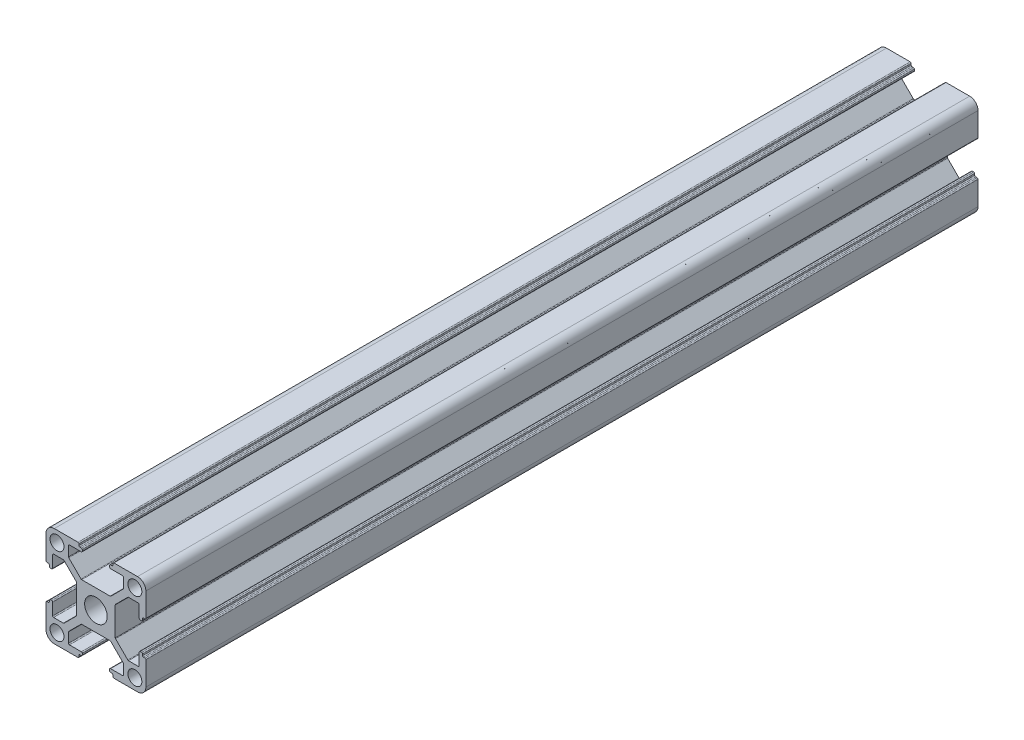
SolidWorks part; units mm, degrees
ref_plane "Alzado" through (0, 0, 0) normal (0, 0, 1) x (1, 0, 0)
ref_plane "Planta" through (0, 0, 0) normal (0, 1, 0) x (1, 0, 0)
ref_plane "Vista lateral" through (0, 0, 0) normal (1, 0, 0) x (0, 0, -1)
ref_plane "Plano1" through (0, 0, -50) normal (0, 0, -1) x (-1, 0, 0)
sketch "Croquis1" plane through (0, 0, -50) normal (0, 0, -1) x (-1, 0, 0)
  line L0 (14.7, -5.1) -> (14.3, -5.1)
  line L1 (14, -4.8) -> (14, -4.4)
  line L2 (13.7, -4.1) -> (13.3, -4.1)
  line L3 (13, -4.4) -> (13, -7.95)
  line L4 (12.7, -8.25) -> (9.7893, -8.25)
  line L5 (9.5772, -8.1622) -> (5.8879, -4.4739)
  line L6 (5.8, -4.2617) -> (5.8, 4.2607)
  line L7 (5.8879, 4.4729) -> (9.5771, 8.1621)
  line L8 (9.7893, 8.25) -> (12.7, 8.25)
  line L9 (13, 7.95) -> (13, 4.4)
  line L10 (13.3, 4.1) -> (13.7, 4.1)
  line L11 (14, 4.4) -> (14, 4.8)
  line L12 (14.3, 5.1) -> (14.7, 5.1)
  line L13 (15, 5.4) -> (15, 12.5)
  line L14 (12.5, 15) -> (5.4, 15)
  line L15 (5.1, 14.7) -> (5.1, 14.3)
  line L16 (4.8, 14) -> (4.4, 14)
  line L17 (4.1, 13.7) -> (4.1, 13.3)
  line L18 (4.4, 13) -> (7.95, 13)
  line L19 (8.25, 12.7) -> (8.25, 9.7883)
  line L20 (8.1621, 9.5761) -> (4.4739, 5.8879)
  line L21 (4.2617, 5.8) -> (-4.2607, 5.8)
  line L22 (-4.4728, 5.8878) -> (-8.1621, 9.5761)
  line L23 (-8.25, 9.7883) -> (-8.25, 12.7)
  line L24 (-7.95, 13) -> (-4.4, 13)
  line L25 (-4.1, 13.3) -> (-4.1, 13.7)
  line L26 (-4.4, 14) -> (-4.8, 14)
  line L27 (-5.1, 14.3) -> (-5.1, 14.7)
  line L28 (-5.4, 15) -> (-12.5, 15)
  line L29 (-15, 12.5) -> (-15, 5.4)
  line L30 (-14.7, 5.1) -> (-14.3, 5.1)
  line L31 (-14, 4.8) -> (-14, 4.4)
  line L32 (-13.7, 4.1) -> (-13.3, 4.1)
  line L33 (-13, 4.4) -> (-13, 7.95)
  line L34 (-12.7, 8.25) -> (-9.7883, 8.25)
  line L35 (-9.5761, 8.1621) -> (-5.8878, 4.4728)
  line L36 (-5.8, 4.2607) -> (-5.8, -4.2617)
  line L37 (-5.8879, -4.4739) -> (-9.5761, -8.1621)
  line L38 (-9.7883, -8.25) -> (-12.7, -8.25)
  line L39 (-13, -7.95) -> (-13, -4.4)
  line L40 (-13.3, -4.1) -> (-13.7, -4.1)
  line L41 (-14, -4.4) -> (-14, -4.8)
  line L42 (-14.3, -5.1) -> (-14.7, -5.1)
  line L43 (-15, -5.4) -> (-15, -12.5)
  line L44 (-12.5, -15) -> (-5.4, -15)
  line L45 (-5.1, -14.7) -> (-5.1, -14.3)
  line L46 (-4.8, -14) -> (-4.4, -14)
  line L47 (-4.1, -13.7) -> (-4.1, -13.3)
  line L48 (-4.4, -13) -> (-7.95, -13)
  line L49 (-8.25, -12.7) -> (-8.25, -9.7893)
  line L50 (-8.1621, -9.5771) -> (-4.4729, -5.8879)
  line L51 (-4.2607, -5.8) -> (4.2617, -5.8)
  line L52 (4.4739, -5.8879) -> (8.1622, -9.5772)
  line L53 (8.25, -9.7893) -> (8.25, -12.7)
  line L54 (7.95, -13) -> (4.4, -13)
  line L55 (4.1, -13.3) -> (4.1, -13.7)
  line L56 (4.4, -14) -> (4.8, -14)
  line L57 (5.1, -14.3) -> (5.1, -14.7)
  line L58 (5.4, -15) -> (12.5, -15)
  line L59 (15, -12.5) -> (15, -5.4)
  arc A0 (15, -5.4) -> (14.7, -5.1) centre (14.7, -5.4) ccw
  arc A1 (14.3, -5.1) -> (14, -4.8) centre (14.3, -4.8) cw
  arc A2 (14, -4.4) -> (13.7, -4.1) centre (13.7, -4.4) ccw
  arc A3 (13.3, -4.1) -> (13, -4.4) centre (13.3, -4.4) ccw
  arc A4 (13, -7.95) -> (12.7, -8.25) centre (12.7, -7.95) cw
  arc A5 (9.7893, -8.25) -> (9.5772, -8.1622) centre (9.7893, -7.95) cw
  arc A6 (5.8879, -4.4739) -> (5.8, -4.2617) centre (6.1, -4.2617) cw
  arc A7 (5.8, 4.2607) -> (5.8879, 4.4729) centre (6.1, 4.2607) cw
  arc A8 (9.5771, 8.1621) -> (9.7893, 8.25) centre (9.7893, 7.95) cw
  arc A9 (12.7, 8.25) -> (13, 7.95) centre (12.7, 7.95) cw
  arc A10 (13, 4.4) -> (13.3, 4.1) centre (13.3, 4.4) ccw
  arc A11 (13.7, 4.1) -> (14, 4.4) centre (13.7, 4.4) ccw
  arc A12 (14, 4.8) -> (14.3, 5.1) centre (14.3, 4.8) cw
  arc A13 (14.7, 5.1) -> (15, 5.4) centre (14.7, 5.4) ccw
  arc A14 (15, 12.5) -> (12.5, 15) centre (12.5, 12.5) ccw
  arc A15 (5.4, 15) -> (5.1, 14.7) centre (5.4, 14.7) ccw
  arc A16 (5.1, 14.3) -> (4.8, 14) centre (4.8, 14.3) cw
  arc A17 (4.4, 14) -> (4.1, 13.7) centre (4.4, 13.7) ccw
  arc A18 (4.1, 13.3) -> (4.4, 13) centre (4.4, 13.3) ccw
  arc A19 (7.95, 13) -> (8.25, 12.7) centre (7.95, 12.7) cw
  arc A20 (8.25, 9.7883) -> (8.1621, 9.5761) centre (7.95, 9.7883) cw
  arc A21 (4.4739, 5.8879) -> (4.2617, 5.8) centre (4.2617, 6.1) cw
  arc A22 (-4.2607, 5.8) -> (-4.4728, 5.8878) centre (-4.2607, 6.1) cw
  arc A23 (-8.1621, 9.5761) -> (-8.25, 9.7883) centre (-7.95, 9.7883) cw
  arc A24 (-8.25, 12.7) -> (-7.95, 13) centre (-7.95, 12.7) cw
  arc A25 (-4.4, 13) -> (-4.1, 13.3) centre (-4.4, 13.3) ccw
  arc A26 (-4.1, 13.7) -> (-4.4, 14) centre (-4.4, 13.7) ccw
  arc A27 (-4.8, 14) -> (-5.1, 14.3) centre (-4.8, 14.3) cw
  arc A28 (-5.1, 14.7) -> (-5.4, 15) centre (-5.4, 14.7) ccw
  arc A29 (-12.5, 15) -> (-15, 12.5) centre (-12.5, 12.5) ccw
  arc A30 (-15, 5.4) -> (-14.7, 5.1) centre (-14.7, 5.4) ccw
  arc A31 (-14.3, 5.1) -> (-14, 4.8) centre (-14.3, 4.8) cw
  arc A32 (-14, 4.4) -> (-13.7, 4.1) centre (-13.7, 4.4) ccw
  arc A33 (-13.3, 4.1) -> (-13, 4.4) centre (-13.3, 4.4) ccw
  arc A34 (-13, 7.95) -> (-12.7, 8.25) centre (-12.7, 7.95) cw
  arc A35 (-9.7883, 8.25) -> (-9.5761, 8.1621) centre (-9.7883, 7.95) cw
  arc A36 (-5.8878, 4.4728) -> (-5.8, 4.2607) centre (-6.1, 4.2607) cw
  arc A37 (-5.8, -4.2617) -> (-5.8879, -4.4739) centre (-6.1, -4.2617) cw
  arc A38 (-9.5761, -8.1621) -> (-9.7883, -8.25) centre (-9.7883, -7.95) cw
  arc A39 (-12.7, -8.25) -> (-13, -7.95) centre (-12.7, -7.95) cw
  arc A40 (-13, -4.4) -> (-13.3, -4.1) centre (-13.3, -4.4) ccw
  arc A41 (-13.7, -4.1) -> (-14, -4.4) centre (-13.7, -4.4) ccw
  arc A42 (-14, -4.8) -> (-14.3, -5.1) centre (-14.3, -4.8) cw
  arc A43 (-14.7, -5.1) -> (-15, -5.4) centre (-14.7, -5.4) ccw
  arc A44 (-15, -12.5) -> (-12.5, -15) centre (-12.5, -12.5) ccw
  arc A45 (-5.4, -15) -> (-5.1, -14.7) centre (-5.4, -14.7) ccw
  arc A46 (-5.1, -14.3) -> (-4.8, -14) centre (-4.8, -14.3) cw
  arc A47 (-4.4, -14) -> (-4.1, -13.7) centre (-4.4, -13.7) ccw
  arc A48 (-4.1, -13.3) -> (-4.4, -13) centre (-4.4, -13.3) ccw
  arc A49 (-7.95, -13) -> (-8.25, -12.7) centre (-7.95, -12.7) cw
  arc A50 (-8.25, -9.7893) -> (-8.1621, -9.5771) centre (-7.95, -9.7893) cw
  arc A51 (-4.4729, -5.8879) -> (-4.2607, -5.8) centre (-4.2607, -6.1) cw
  arc A52 (4.2617, -5.8) -> (4.4739, -5.8879) centre (4.2617, -6.1) cw
  arc A53 (8.1622, -9.5772) -> (8.25, -9.7893) centre (7.95, -9.7893) cw
  arc A54 (8.25, -12.7) -> (7.95, -13) centre (7.95, -12.7) cw
  arc A55 (4.4, -13) -> (4.1, -13.3) centre (4.4, -13.3) ccw
  arc A56 (4.1, -13.7) -> (4.4, -14) centre (4.4, -13.7) ccw
  arc A57 (4.8, -14) -> (5.1, -14.3) centre (4.8, -14.3) cw
  arc A58 (5.1, -14.7) -> (5.4, -15) centre (5.4, -14.7) ccw
  arc A59 (12.5, -15) -> (15, -12.5) centre (12.5, -12.5) ccw
  circle A60 centre (-11.7, 11.7) radius 2.1
  circle A61 centre (-11.7, -11.7) radius 2.1
  circle A62 centre (0, 0) radius 3.4
  circle A63 centre (11.7, 11.7) radius 2.1
  circle A64 centre (11.7, -11.7) radius 2.1
extrude "Saliente-Extruir1" add sketch "Croquis1" against normal blind 400
sketch "Croquis3" plane through (0, 0, -50) normal (0, 0, -1) x (-1, 0, 0)
  line L1 (-17.8618, 16.2307) -> (19.0298, 16.2307)
  line L2 (-17.8618, 16.2307) -> (-17.8618, -15.6266)
  line L3 (-17.8618, -15.6266) -> (19.0298, -15.6266)
  line L4 (19.0298, 16.2307) -> (19.0298, -15.6266)
extrude "Cortar-Extruir2" cut sketch "Croquis3" against normal blind 150
